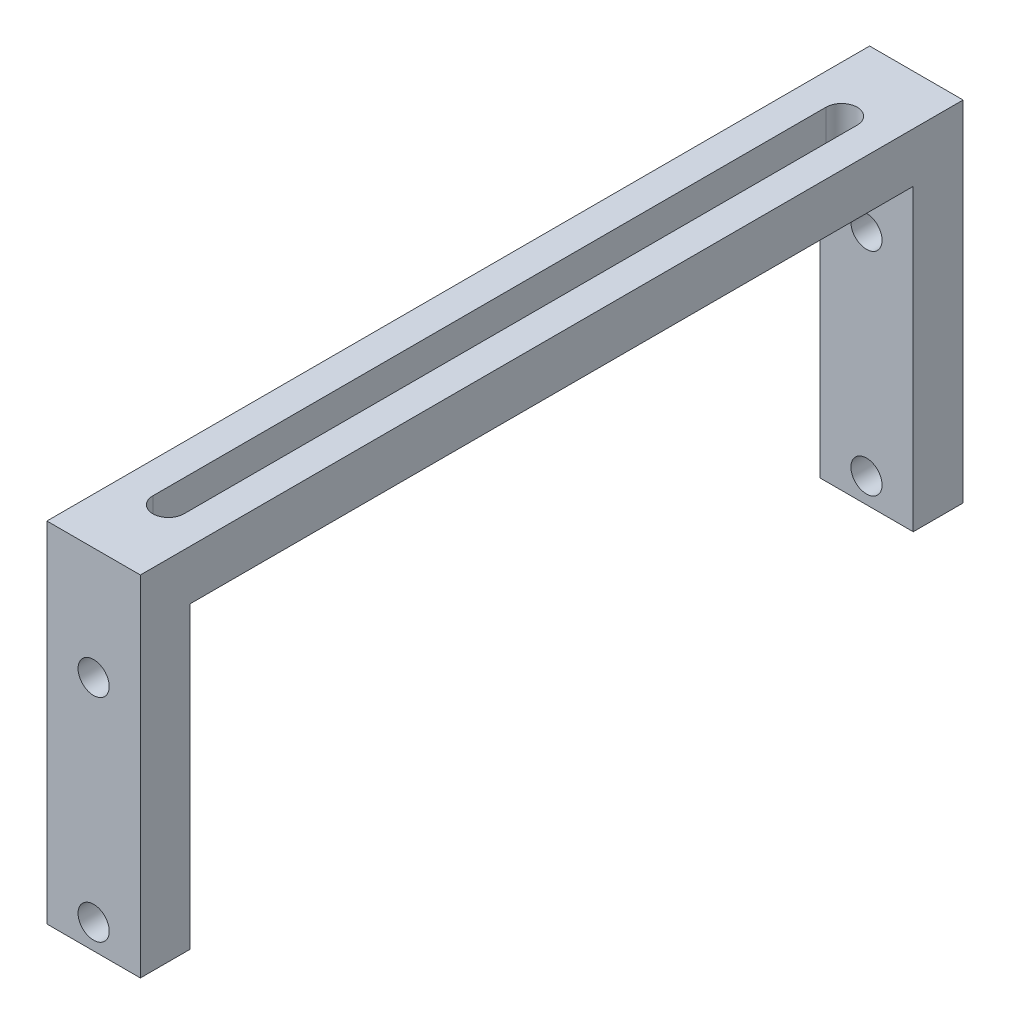
SolidWorks part; units mm, degrees
ref_plane "Front Plane" through (0, 0, 0) normal (0, 0, 1) x (1, 0, 0)
ref_plane "Top Plane" through (0, 0, 0) normal (0, 1, 0) x (1, 0, 0)
ref_plane "Right Plane" through (0, 0, 0) normal (1, 0, 0) x (0, 0, -1)
sketch "Sketch1" plane through (0, 0, 0) normal (0, 0, 1) x (1, 0, 0)
  line L1 (4.7625, 17.78) -> (-4.7625, 17.78)
  line L2 (4.7625, 17.78) -> (4.7625, -17.78)
  line L3 (4.7625, -17.78) -> (-4.7625, -17.78)
  line L4 (-4.7625, 17.78) -> (-4.7625, -17.78)
  line L5 (4.7625, 17.78) -> (-4.7625, -17.78) construction
  line L6 (4.7625, -17.78) -> (-4.7625, 17.78) construction
  point P0 (0, 0)
  dimension "D1" = 35.56
  dimension "D2" = 9.525
extrude "Boss-Extrude1" add sketch "Sketch1" along normal blind 83.82
sketch "Sketch2" plane through (4.7625, 0, 0) normal (1, 0, 0) x (0, 0, -1)
  line L0 (-83.82, -17.78) -> (0, -17.78) construction
  line L1 (-78.74, 12.7) -> (-5.08, 12.7)
  line L2 (-78.74, 12.7) -> (-78.74, -17.78)
  line L3 (-78.74, -17.78) -> (-5.08, -17.78)
  line L4 (-5.08, 12.7) -> (-5.08, -17.78)
  line L5 (-83.82, -17.78) -> (-83.82, 17.78) construction
  line L7 (-83.82, 13.4787) -> (0, 13.4787) construction
  line L8 (0, -17.78) -> (0, 17.78) construction
  line L9 (-83.82, 17.78) -> (0, 17.78) construction
  point P12 (-41.91, 12.7)
  point P13 (-41.91, 13.4787)
  dimension "D1" = 5.08
  dimension "D2" = 5.08
extrude "Cut-Extrude1" cut sketch "Sketch2" against normal blind 78.74
sketch "Sketch3" plane through (0, 17.78, 0) normal (0, 1, 0) x (1, 0, 0)
  line L0 (-1.5875, -76.2) -> (-1.5875, -7.62)
  line L1 (1.5875, -7.62) -> (1.5875, -76.2)
  line L2 (-4.7625, -12.4581) -> (4.7625, -12.4581) construction
  line L3 (-4.7625, -83.82) -> (-4.7625, 0) construction
  line L4 (4.7625, -83.82) -> (4.7625, 0) construction
  line L5 (4.7625, -83.82) -> (-4.7625, -83.82) construction
  line L6 (4.7625, 0) -> (-4.7625, 0) construction
  arc A0 (-1.5875, -7.62) -> (1.5875, -7.62) centre (0, -7.62) cw
  arc A1 (-1.5875, -76.2) -> (1.5875, -76.2) centre (0, -76.2) ccw
  point P12 (0, -12.4581)
  dimension "D1" = 3.175
  dimension "D2" = 7.62
  dimension "D3" = 7.62
extrude "Cut-Extrude2" cut sketch "Sketch3" against normal blind 78.74
sketch "Sketch4" plane through (0, 0, 83.82) normal (0, 0, 1) x (1, 0, 0)
  line L0 (-4.7625, -17.78) -> (4.7625, -17.78) construction
  line L1 (-4.7625, -3.841) -> (4.7625, -3.841) construction
  line L2 (-4.7625, 17.78) -> (-4.7625, -17.78) construction
  line L3 (4.7625, -17.78) -> (4.7625, 17.78) construction
  circle A0 centre (0, -15.24) radius 1.5875
  point P10 (0, -3.841)
  dimension "D1" = 3.175
  dimension "D2" = 2.54
extrude "Cut-Extrude3" cut sketch "Sketch4" against normal through all
sketch "Sketch5" plane through (0, 0, 83.82) normal (0, 0, 1) x (1, 0, 0)
  line L0 (-4.7625, -17.78) -> (4.7625, -17.78) construction
  circle A0 centre (0, 6.35) radius 1.5875
  point P4 (0, 0)
  dimension "D1" = 3.175
  dimension "D2" = 24.13
extrude "Cut-Extrude4" cut sketch "Sketch5" against normal through all
